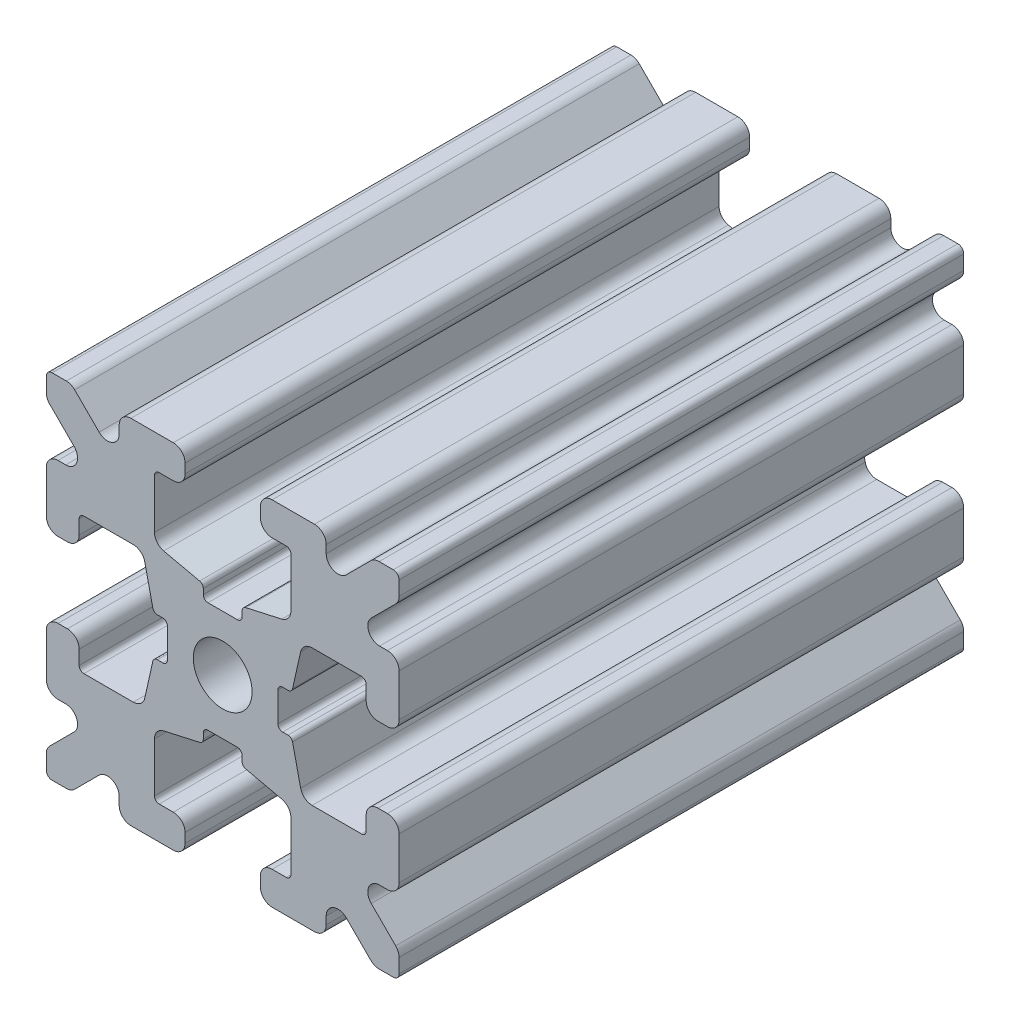
SolidWorks part; units mm, degrees
ref_plane "Front Plane" through (0, 0, 0) normal (0, 0, 1) x (1, 0, 0)
ref_plane "Top Plane" through (0, 0, 0) normal (0, 1, 0) x (1, 0, 0)
ref_plane "Right Plane" through (0, 0, 0) normal (1, 0, 0) x (0, 0, -1)
sketch "Sketch1" plane through (0, 0, 0) normal (0, 0, 1) x (1, 0, 0)
  line L1 (-7.5, -7.5) -> (7.5, -7.5)
  line L2 (-7.5, -7.5) -> (-7.5, 7.5)
  line L3 (-7.5, 7.5) -> (7.5, 7.5)
  line L4 (7.5, -7.5) -> (7.5, 7.5)
  line L5 (-7.5, -7.5) -> (7.5, 7.5) construction
  line L6 (-7.5, 7.5) -> (7.5, -7.5) construction
  circle A0 centre (0, 0) radius 1.25
  point P0 (0, 0)
  dimension "D2" = 2.5
  dimension "D1" = 15
extrude "Boss-Extrude1" add sketch "Sketch1" along normal mid plane 24
fillet "Fillet1" radius 0.25 4 edges at (7.5, -7.5, 0) (-7.5, -7.5, 0) (7.5, 7.5, 0) (-7.5, 7.5, 0)
sketch "Sketch2" plane through (0, 0, 12) normal (0, 0, 1) x (1, 0, 0)
  line L0 (-7.5, 7.25) -> (-7.5, -7.25) construction
  line L1 (-7.5, 1.6) -> (-6.1, 1.6)
  line L2 (-7.5, 1.6) -> (-7.5, -1.6)
  line L3 (-7.5, -1.6) -> (-6.1, -1.6)
  line L4 (-6.1, 1.6) -> (-6.1, 2.9)
  line L5 (0, 0) -> (-12.1036, 0) construction
  line L6 (-6.1, -2.9) -> (-3.4, -2.9)
  line L7 (0, 0) -> (-7.25, 7.25) construction
  line L8 (-6.1, 2.9) -> (-3.4, 2.9)
  line L9 (-3.4, -2.9) -> (-3.4, 2.9)
  line L10 (55, 0) -> (-55, 0) construction
  line L11 (-6.1, -2.9) -> (-6.1, -1.6)
  line L12 (2.9, 6.1) -> (1.6, 6.1)
  line L13 (2.9, 3.4) -> (-2.9, 3.4)
  line L14 (-2.9, 6.1) -> (-2.9, 3.4)
  line L15 (2.9, 6.1) -> (2.9, 3.4)
  line L16 (-1.6, 6.1) -> (-2.9, 6.1)
  line L17 (1.6, 7.5) -> (1.6, 6.1)
  line L18 (-1.6, 7.5) -> (1.6, 7.5)
  line L19 (-1.6, 7.5) -> (-1.6, 6.1)
  line L20 (-1.6, -7.5) -> (-1.6, -6.1)
  line L21 (-1.6, -7.5) -> (1.6, -7.5)
  line L22 (1.6, -7.5) -> (1.6, -6.1)
  line L23 (-1.6, -6.1) -> (-2.9, -6.1)
  line L24 (2.9, -6.1) -> (2.9, -3.4)
  line L25 (-2.9, -6.1) -> (-2.9, -3.4)
  line L26 (2.9, -3.4) -> (-2.9, -3.4)
  line L27 (2.9, -6.1) -> (1.6, -6.1)
  line L28 (6.1, -2.9) -> (6.1, -1.6)
  line L29 (3.4, -2.9) -> (3.4, 2.9)
  line L30 (6.1, 2.9) -> (3.4, 2.9)
  line L31 (6.1, -2.9) -> (3.4, -2.9)
  line L32 (6.1, 1.6) -> (6.1, 2.9)
  line L33 (7.5, -1.6) -> (6.1, -1.6)
  line L34 (7.5, 1.6) -> (7.5, -1.6)
  line L35 (7.5, 1.6) -> (6.1, 1.6)
  dimension "D1" = 3.2
  dimension "D2" = 5.8
  dimension "D3" = 1.4
  dimension "D4" = 2.7
extrude "Cut-Extrude1" cut sketch "Sketch2" against normal through all
sketch "Sketch4" plane through (0, 0, 12) normal (0, 0, 1) x (1, 0, 0)
  line L0 (-3.4, 2.9) -> (-2.75, 0)
  line L1 (55, 0) -> (-55, 0) construction
  line L2 (-2.75, 0) -> (-3.4, -2.9)
  line L3 (-3.4, -2.9) -> (-3.4, 2.9) construction
  line L4 (-3.4, 2.9) -> (-3.4, -2.9)
  line L5 (-2.9, 3.4) -> (0, 2.75)
  line L6 (0, 2.75) -> (2.9, 3.4)
  line L7 (2.9, 3.4) -> (-2.9, 3.4)
  line L8 (3.4, 2.9) -> (2.75, 0)
  line L9 (2.75, 0) -> (3.4, -2.9)
  line L10 (3.4, -2.9) -> (3.4, 2.9)
  line L11 (-2.9, -3.4) -> (0, -2.75)
  line L12 (0, -2.75) -> (2.9, -3.4)
  line L13 (2.9, -3.4) -> (-2.9, -3.4)
  circle A2 centre (0, 0) radius 2.75
  circle A3 centre (0, 0) radius 2.75 construction
  dimension "D1" = 1.5
extrude "Cut-Extrude3" cut sketch "Sketch4" against normal through all
fillet "Fillet3" radius 0.5 16 edges at (-6.1, -1.6, 0) (-7.5, -1.6, 0) (-6.1, 1.6, 0) (-7.5, 1.6, 0) (-1.6, -7.5, 0) (-1.6, -6.1, 0) (1.6, -7.5, 0) (1.6, -6.1, 0) (6.1, -1.6, 0) (7.5, -1.6, 0) (7.5, 1.6, 0) (6.1, 1.6, 0) (1.6, 7.5, 0) (1.6, 6.1, 0) (-1.6, 7.5, 0) (-1.6, 6.1, 0)
fillet "Fillet4" radius 0.5 8 edges at (-3.4, 2.9, 0) (-3.4, -2.9, 0) (2.9, -3.4, 0) (-2.9, -3.4, 0) (3.4, -2.9, 0) (3.4, 2.9, 0) (-2.9, 3.4, 0) (2.9, 3.4, 0)
fillet "Fillet5" radius 3 4 edges at (0, -2.75, 0) (2.75, 0, 0) (-2.75, 0, 0) (0, 2.75, 0)
fillet "Fillet6" radius 0.2 8 edges at (-2.9, -6.1, 0) (2.9, -6.1, 0) (6.1, -2.9, 0) (6.1, 2.9, 0) (2.9, 6.1, 0) (-2.9, 6.1, 0) (-6.1, -2.9, 0) (-6.1, 2.9, 0)
sketch "Sketch5" plane through (0, 0, 12) normal (0, 0, 1) x (1, 0, 0)
  line L0 (0, 0) -> (-7.25, 7.25) construction
  line L1 (-7.5, 6.4393) -> (-5.4607, 4.4)
  line L2 (-6.4393, 7.5) -> (-4.4, 5.4607)
  line L3 (-7.5, 4.4) -> (-5.4607, 4.4)
  line L4 (-3.8003, 2.9) -> (-5.9, 2.9) construction
  line L5 (0, 0) -> (-12.1819, 0) construction
  line L6 (-4.4, 7.5) -> (-4.4, 5.4607)
  line L7 (-2.9, 5.9) -> (-2.9, 3.8003) construction
  line L8 (-7.5, 6.4393) -> (-7.5, 4.4)
  line L9 (-7.5, 7.25) -> (-7.5, 2.1) construction
  line L10 (2.1, -7.5) -> (7.25, -7.5) construction
  line L11 (7.5, -7.25) -> (7.5, -2.1) construction
  line L12 (7.25, 7.5) -> (2.1, 7.5) construction
  line L13 (-2.1, 7.5) -> (-7.25, 7.5) construction
  line L14 (-4.4, 7.5) -> (-6.4393, 7.5)
  line L16 (55, 0) -> (-55, 0) construction
  line L17 (0, 0) -> (0, 10.993) construction
  line L18 (0, -54.6431) -> (0, 54.6431) construction
  line L20 (4.4, 7.5) -> (6.4393, 7.5)
  line L22 (7.5, 6.4393) -> (7.5, 4.4)
  line L23 (4.4, 7.5) -> (4.4, 5.4607)
  line L24 (7.5, 4.4) -> (5.4607, 4.4)
  line L25 (6.4393, 7.5) -> (4.4, 5.4607)
  line L26 (7.5, 6.4393) -> (5.4607, 4.4)
  line L27 (7.5, -6.4393) -> (5.4607, -4.4)
  line L28 (6.4393, -7.5) -> (4.4, -5.4607)
  line L29 (7.5, -4.4) -> (5.4607, -4.4)
  line L30 (4.4, -7.5) -> (4.4, -5.4607)
  line L31 (7.5, -6.4393) -> (7.5, -4.4)
  line L33 (4.4, -7.5) -> (6.4393, -7.5)
  line L36 (-4.4, -7.5) -> (-6.4393, -7.5)
  line L38 (-7.5, -6.4393) -> (-7.5, -4.4)
  line L39 (-4.4, -7.5) -> (-4.4, -5.4607)
  line L40 (-7.5, -4.4) -> (-5.4607, -4.4)
  line L41 (-6.4393, -7.5) -> (-4.4, -5.4607)
  line L42 (-7.5, -6.4393) -> (-5.4607, -4.4)
  dimension "D1" = 1.5
  dimension "D2" = 1.5
  dimension "D3" = 1.5
extrude "Cut-Extrude4" cut sketch "Sketch5" against normal through all
fillet "Fillet8" radius 0.5 24 edges at (-5.4607, 4.4, 0) (-7.5, 4.4, 0) (-5.4607, -4.4, 0) (-7.5, -4.4, 0) (-4.4, -7.5, 0) (-4.4, -5.4607, 0) (4.4, -7.5, 0) (4.4, -5.4607, 0) (5.4607, -4.4, 0) (7.5, -4.4, 0) (7.5, 4.4, 0) (5.4607, 4.4, 0) (4.4, 5.4607, 0) (4.4, 7.5, 0) (-4.4, 5.4607, 0) (-4.4, 7.5, 0) (-6.4393, 7.5, 0) (-7.5, 6.4393, 0) (6.4393, 7.5, 0) (7.5, 6.4393, 0) (6.4393, -7.5, 0) (7.5, -6.4393, 0) (-6.4393, -7.5, 0) (-7.5, -6.4393, 0)
sketch "Sketch6" plane through (0, 0, 12) normal (0, 0, 1) x (1, 0, 0)
  line L0 (0, 0) -> (0, 11.013) construction
  line L1 (0.6561, 2.8971) -> (2.1235, 2.8971) construction
  line L2 (0, -54.6431) -> (0, 54.6431) construction
  line L3 (0, 0) -> (7.25, 7.25) construction
  line L4 (7.5, 0.8255) -> (7.5, -0.8255)
  line L5 (2.3471, 0.8255) -> (7.5, 0.8255)
  line L6 (0, 0) -> (12.4016, 0) construction
  line L7 (0.8255, -7.5) -> (-0.8255, -7.5)
  line L8 (2.3471, -0.8255) -> (2.3471, 0.8255)
  line L9 (0.8255, -2.3471) -> (0.8255, -7.5)
  line L10 (7.5, -0.8255) -> (2.3471, -0.8255)
  line L11 (-7.5, -0.8255) -> (-2.3471, -0.8255)
  line L12 (-2.3471, -0.8255) -> (-2.3471, 0.8255)
  line L13 (-0.8255, -2.3471) -> (0.8255, -2.3471)
  line L14 (-0.8255, 7.5) -> (-0.8255, 2.3471)
  line L15 (-0.8255, 2.3471) -> (0.8255, 2.3471)
  line L16 (-0.8255, -7.5) -> (-0.8255, -2.3471)
  line L17 (0.8255, 2.3471) -> (0.8255, 7.5)
  line L18 (0.8255, 7.5) -> (-0.8255, 7.5)
  line L19 (3.9, 7.5) -> (2.1, 7.5) construction
  line L20 (-2.3471, 0.8255) -> (-7.5, 0.8255)
  line L21 (-7.5, 0.8255) -> (-7.5, -0.8255)
  point P5 (0, -2.5973)
  point P7 (0, 2.5973)
  dimension "D3" = 0.55
  dimension "D1" = 1.651
extrude "Cut-Extrude5" cut sketch "Sketch6" against normal through all
fillet "Fillet10" radius 0.2 16 edges at (-2.935, 0.8255, 0) (-2.935, -0.8255, 0) (2.935, -0.8255, 0) (2.935, 0.8255, 0) (0.8255, 2.935, 0) (-0.8255, 2.935, 0) (-2.3471, 0.8255, 0) (-2.3471, -0.8255, 0) (0.8255, 2.3471, 0) (-0.8255, 2.3471, 0) (2.3471, 0.8255, 0) (2.3471, -0.8255, 0) (0.8255, -2.935, 0) (0.8255, -2.3471, 0) (-0.8255, -2.3471, 0) (-0.8255, -2.935, 0)
